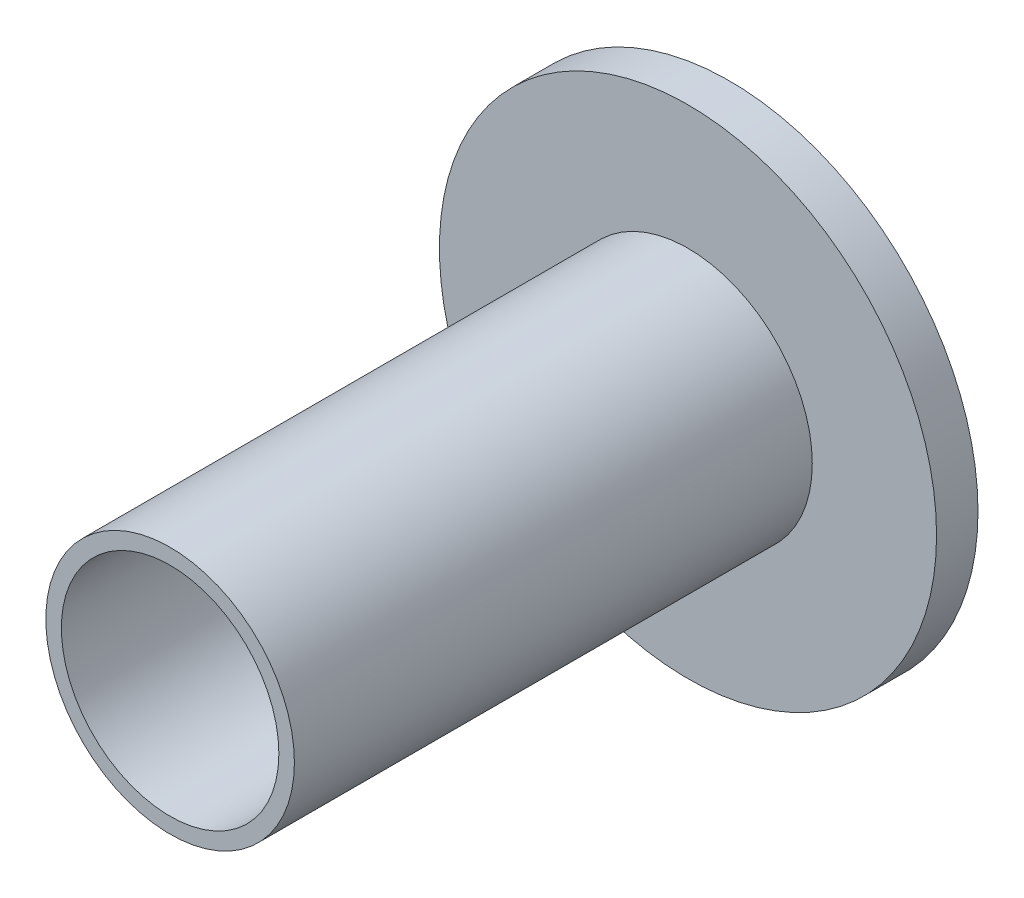
SolidWorks part; units mm, degrees
ref_plane "Ön Düzlem" through (0, 0, 0) normal (0, 0, 1) x (1, 0, 0)
ref_plane "Üst Düzlem" through (0, 0, 0) normal (0, 1, 0) x (1, 0, 0)
ref_plane "Sağ Düzlem" through (0, 0, 0) normal (1, 0, 0) x (0, 0, -1)
sketch "Çizim1" plane through (0, 0, 0) normal (0, 0, 1) x (1, 0, 0)
  circle A0 centre (0, 0) radius 12
  dimension "D2" = 24
extrude "Yükseklik-Ekstrüzyon1" add sketch "Çizim1" along normal blind 2
sketch "Çizim2" plane through (0, 0, 2) normal (0, 0, 1) x (1, 0, 0)
  circle A0 centre (0, 0) radius 6
  dimension "D1" = 12
extrude "Yükseklik-Ekstrüzyon2" add sketch "Çizim2" along normal blind 25
sketch "Çizim3" plane through (0, 0, 27) normal (0, 0, 1) x (1, 0, 0)
  circle A0 centre (0, 0) radius 5.25
  dimension "D1" = 10.5
extrude "Kes-Ekstrüzyon1" cut sketch "Çizim3" against normal blind 37
